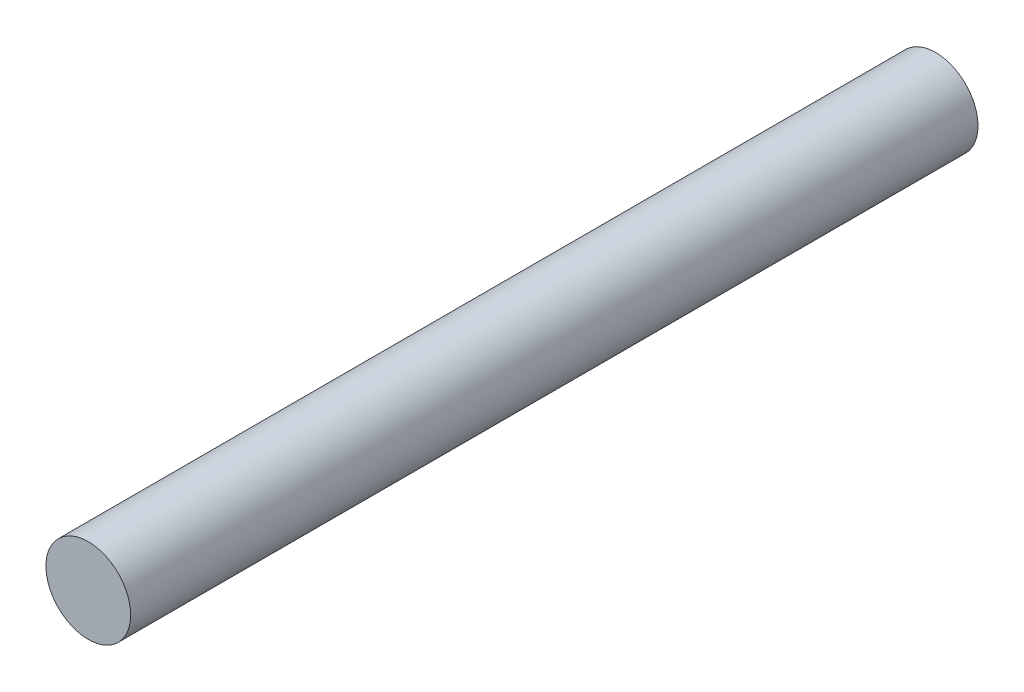
SolidWorks part; units mm, degrees
ref_plane "Front Plane" through (0, 0, 0) normal (0, 0, 1) x (1, 0, 0)
ref_plane "Top Plane" through (0, 0, 0) normal (0, 1, 0) x (1, 0, 0)
ref_plane "Right Plane" through (0, 0, 0) normal (1, 0, 0) x (0, 0, -1)
sketch "Sketch1" plane through (0, 0, 0) normal (0, 0, 1) x (1, 0, 0)
  circle A0 centre (0, 0) radius 0.5
  dimension "D1" = 1
extrude "Boss-Extrude1" add sketch "Sketch1" along normal blind 10
